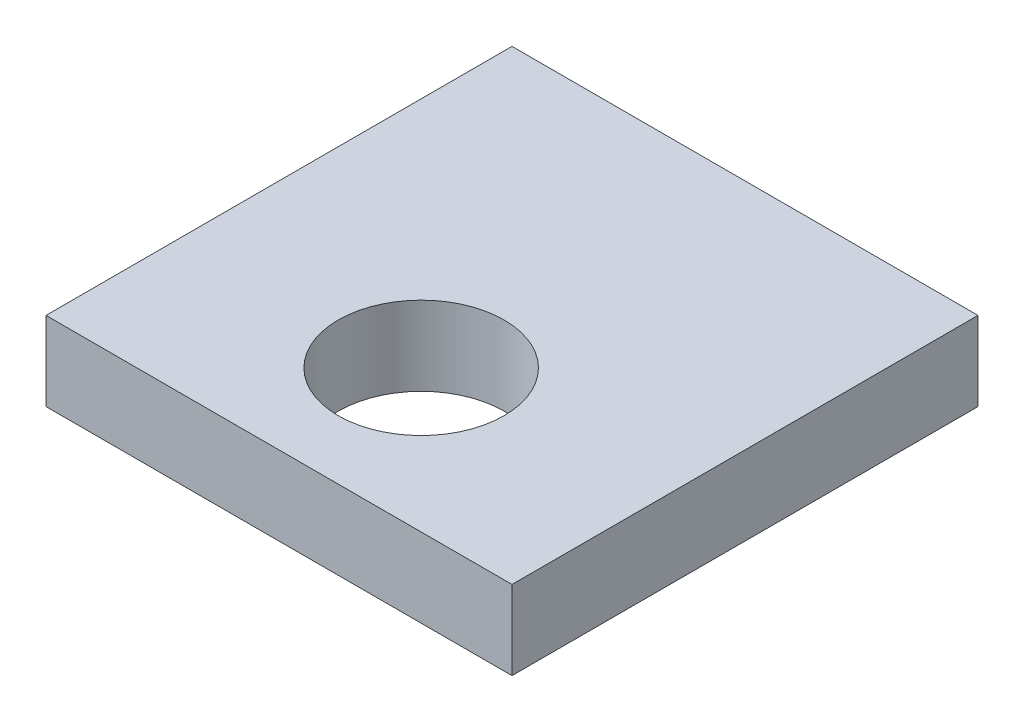
SolidWorks part; units mm, degrees
ref_plane "Plan de face" through (0, 0, 0) normal (0, 0, 1) x (1, 0, 0)
ref_plane "Plan de dessus" through (0, 0, 0) normal (0, 1, 0) x (1, 0, 0)
ref_plane "Plan de droite" through (0, 0, 0) normal (1, 0, 0) x (0, 0, -1)
sketch "Esquisse1" plane through (0, 0, 0) normal (0, 1, 0) x (1, 0, 0)
  line L0 (-41.2737, -18.7654) -> (-11.7737, -18.7654) construction
  line L1 (-41.2737, 22.2346) -> (17.7263, 22.2346)
  line L2 (-41.2737, 22.2346) -> (-41.2737, -36.7654)
  line L3 (-41.2737, -36.7654) -> (17.7263, -36.7654)
  line L4 (17.7263, 22.2346) -> (17.7263, -36.7654)
  line L5 (-11.7737, -18.7654) -> (-11.7737, 22.2346) construction
  line L6 (17.7263, -18.7654) -> (-11.7737, -18.7654) construction
  line L7 (-11.7737, -18.7654) -> (-11.7737, -36.7654) construction
  circle A0 centre (-11.7737, -18.7654) radius 10.5
  dimension "D3" = 18
  dimension "D4" = 21
  dimension "D1" = 59
  dimension "D2" = 59
extrude "Boss.-Extru.2" add sketch "Esquisse1" along normal blind 10
